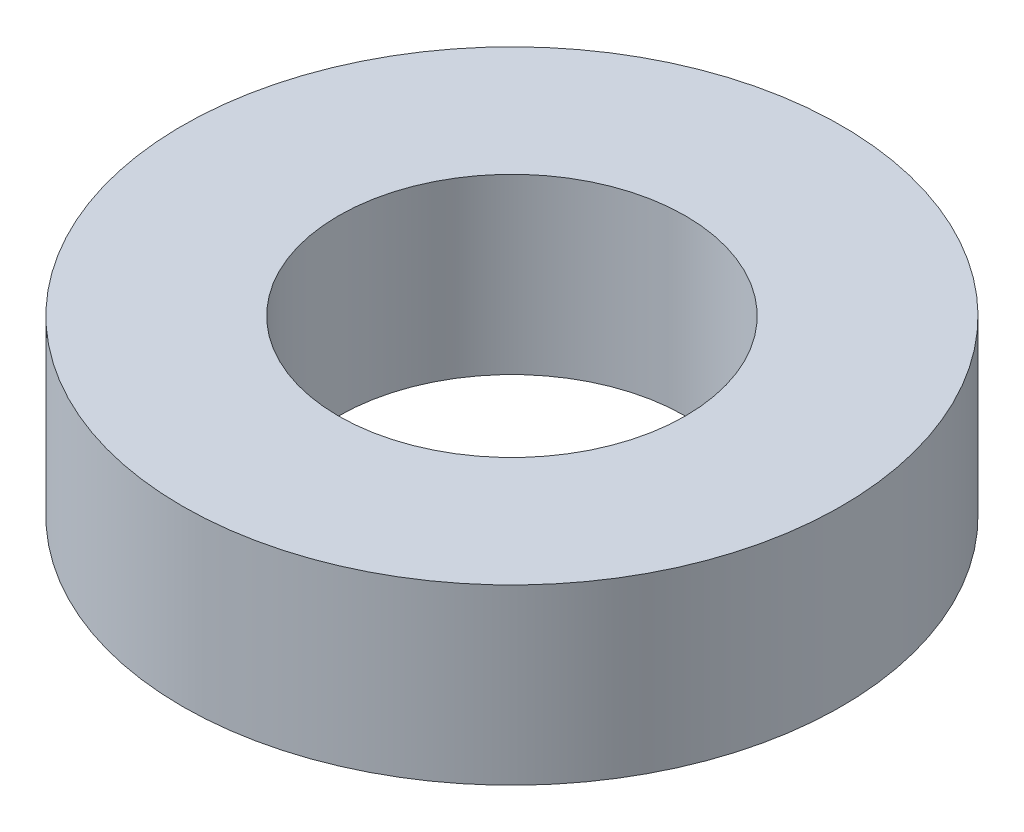
SolidWorks part; units mm, degrees
material "AISI 1035 钢 (SS)"
ref_plane "前视基准面" through (0, 0, 0) normal (0, 0, 1) x (1, 0, 0)
ref_plane "上视基准面" through (0, 0, 0) normal (0, 1, 0) x (1, 0, 0)
ref_plane "右视基准面" through (0, 0, 0) normal (1, 0, 0) x (0, 0, -1)
sketch "草图1" plane through (0, 0, 0) normal (0, 1, 0) x (1, 0, 0)
  circle A0 centre (0, 0) radius 5
  circle A1 centre (0, 0) radius 9.5
  dimension "D1" = 10
  dimension "D2" = 19
extrude "凸台-拉伸1" add sketch "草图1" along normal blind 5
